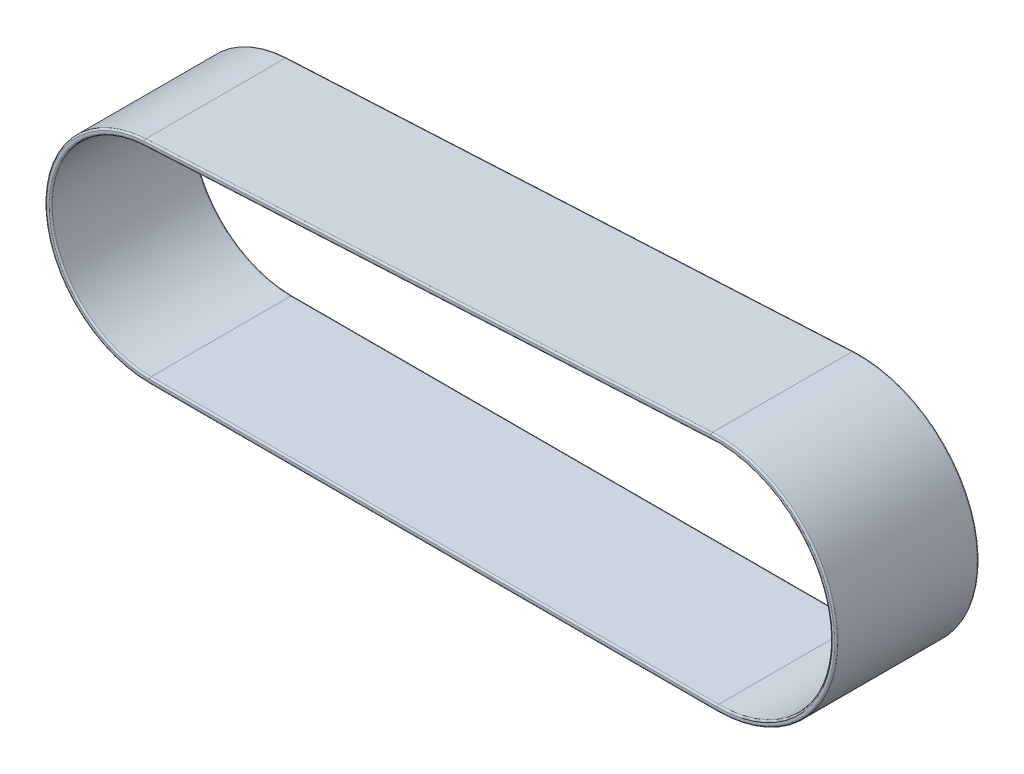
SolidWorks part; units mm, degrees
ref_plane "Front Plane" through (0, 0, 0) normal (0, 0, 1) x (1, 0, 0)
ref_plane "Top Plane" through (0, 0, 0) normal (0, 1, 0) x (1, 0, 0)
ref_plane "Right Plane" through (0, 0, 0) normal (1, 0, 0) x (0, 0, -1)
sketch "Sketch1" plane through (0, 0, 0) normal (0, 0, 1) x (1, 0, 0)
  line L0 (-175, 0) -> (175, 0)
  line L1 (171.4024, 139.9075) -> (-178.1351, 121.9194)
  line L2 (-175, -3.5) -> (175, -3.5)
  line L3 (171.2225, 143.4029) -> (-178.315, 125.4148)
  arc A0 (175, 0) -> (171.4024, 139.9075) centre (175, 70) ccw
  arc A1 (-178.1351, 121.9194) -> (-175, 0) centre (-175, 61) ccw
  arc A2 (175, -3.5) -> (171.2225, 143.4029) centre (175, 70) ccw
  arc A3 (-178.315, 125.4148) -> (-175, -3.5) centre (-175, 61) ccw
  point P5 (0, 0)
  dimension "D1" = 70
  dimension "D3" = 61
  dimension "D2" = 350
  dimension "D4" = 3.5
extrude "Boss-Extrude1" add sketch "Sketch1" along normal blind 88
fillet "Fillet1" radius 1 16 edges at (0, -3.5, 88) (0, -3.5, 0) (-3.3663, 130.9134, 88) (-3.3663, 130.9134, 0) (-3.5462, 134.4088, 88) (-3.5462, 134.4088, 0) (244.9769, 71.7994, 88) (244.9769, 71.7994, 0) (-239.4787, 59.342, 88) (-239.4787, 59.342, 0) (248.4757, 71.8894, 88) (248.4757, 71.8894, 0) (-235.9798, 59.4319, 88) (-235.9798, 59.4319, 0) (0, 0, 88) (0, 0, 0)
